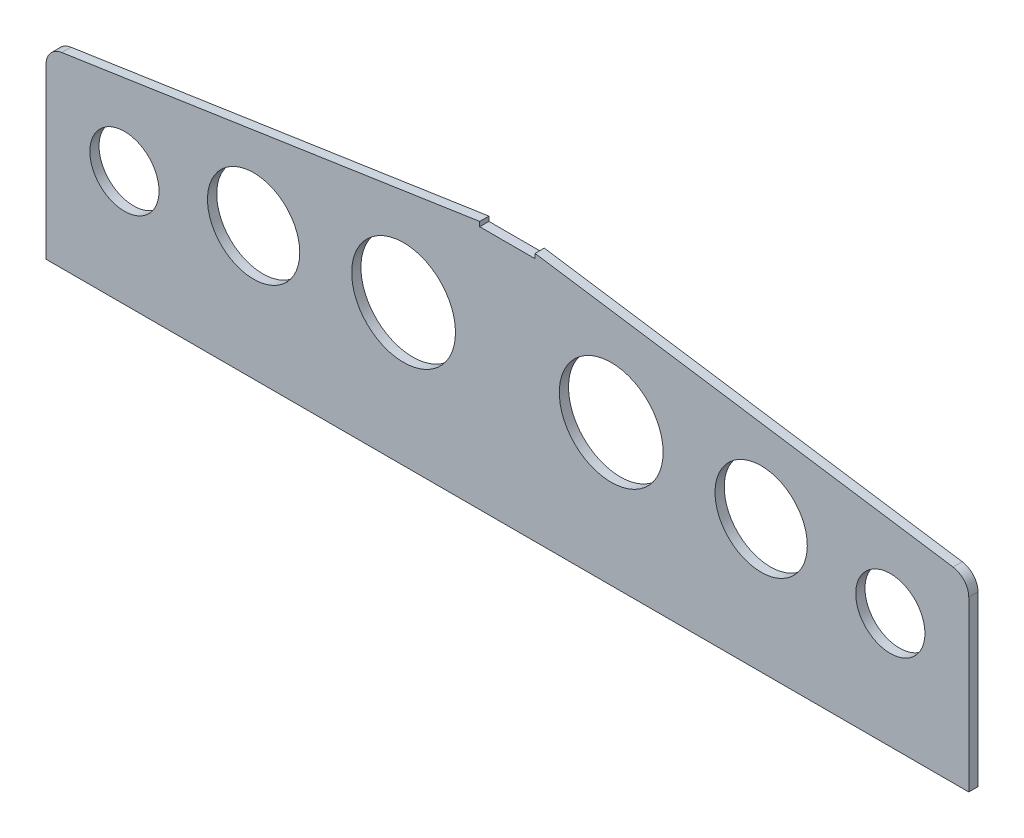
SolidWorks part; units mm, degrees
ref_plane "前视基准面" through (0, 0, 0) normal (0, 0, 1) x (1, 0, 0)
ref_plane "上视基准面" through (0, 0, 0) normal (0, 1, 0) x (1, 0, 0)
ref_plane "右视基准面" through (0, 0, 0) normal (1, 0, 0) x (0, 0, -1)
sketch "草图1" plane through (0, 0, 0) normal (0, 0, 1) x (1, 0, 0)
  line L0 (-315.6389, 504.0667) -> (-315.6389, 430.9562)
  line L1 (84.3611, 504.0667) -> (84.3611, 430.9562)
  line L2 (-315.6389, 430.9562) -> (84.3611, 430.9562)
  line L3 (-103.6389, 539.1562) -> (77.5478, 511.9782)
  line L4 (-127.6389, 539.1562) -> (-308.8256, 511.9782)
  line L5 (-127.6389, 539.1562) -> (-127.6389, 537.1562)
  line L6 (-103.6389, 539.1562) -> (-103.6389, 537.1562)
  line L7 (-127.6389, 537.1562) -> (-103.6389, 537.1562)
  arc A0 (-308.8256, 511.9782) -> (-315.6389, 504.0667) centre (-307.6389, 504.0667) ccw
  arc A1 (84.3611, 504.0667) -> (77.5478, 511.9782) centre (76.3611, 504.0667) ccw
  circle A2 centre (50.3611, 480.9562) radius 15
  circle A3 centre (-5.6389, 488.4562) radius 20
  circle A4 centre (-70.6389, 492.2062) radius 22.5
  circle A5 centre (-281.6389, 480.9562) radius 15
  circle A6 centre (-225.6389, 488.4562) radius 20
  circle A7 centre (-160.6389, 492.2062) radius 22.5
extrude "凸台-拉伸1" add sketch "草图1" along normal blind 4
